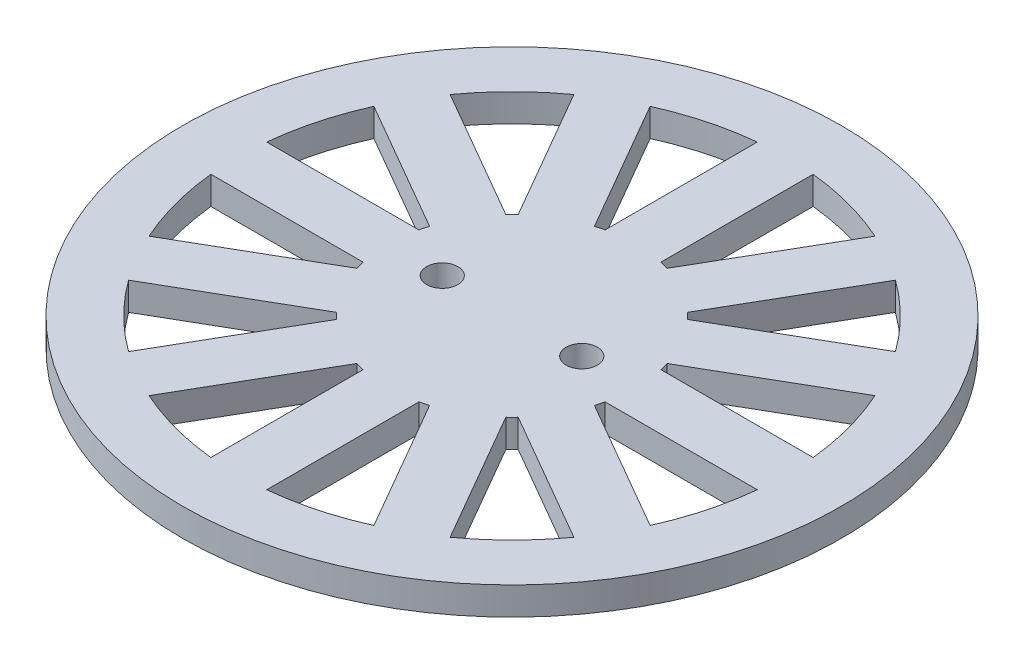
SolidWorks part; units mm, degrees
ref_plane "Front Plane" through (0, 0, 0) normal (0, 0, 1) x (1, 0, 0)
ref_plane "Top Plane" through (0, 0, 0) normal (0, 1, 0) x (1, 0, 0)
ref_plane "Right Plane" through (0, 0, 0) normal (1, 0, 0) x (0, 0, -1)
sketch "Sketch1" plane through (0, 0, 0) normal (0, 1, 0) x (1, 0, 0)
  line L0 (-2.54, 24.8706) -> (-2.54, 11.0171)
  line L1 (2.54, 24.8706) -> (2.54, 11.0171)
  line L2 (10.2356, 22.8086) -> (3.3089, 10.8111)
  line L3 (14.635, 20.2686) -> (7.7083, 8.2711)
  line L4 (20.2686, 14.635) -> (8.2711, 7.7083)
  line L5 (22.8086, 10.2356) -> (10.8111, 3.3089)
  line L6 (24.8706, 2.54) -> (11.0171, 2.54)
  line L7 (24.8706, -2.54) -> (11.0171, -2.54)
  line L8 (22.8086, -10.2356) -> (10.8111, -3.3089)
  line L9 (20.2686, -14.635) -> (8.2711, -7.7083)
  line L10 (14.635, -20.2686) -> (7.7083, -8.2711)
  line L11 (10.2356, -22.8086) -> (3.3089, -10.8111)
  line L12 (2.54, -24.8706) -> (2.54, -11.0171)
  line L13 (-2.54, -24.8706) -> (-2.54, -11.0171)
  line L14 (-10.2356, -22.8086) -> (-3.3089, -10.8111)
  line L15 (-14.635, -20.2686) -> (-7.7083, -8.2711)
  line L16 (-20.2686, -14.635) -> (-8.2711, -7.7083)
  line L17 (-22.8086, -10.2356) -> (-10.8111, -3.3089)
  line L18 (-24.8706, -2.54) -> (-11.0171, -2.54)
  line L19 (-24.8706, 2.54) -> (-11.0171, 2.54)
  line L20 (-22.8086, 10.2356) -> (-10.8111, 3.3089)
  line L21 (-20.2686, 14.635) -> (-8.2711, 7.7083)
  line L22 (-14.635, 20.2686) -> (-7.7083, 8.2711)
  line L23 (-10.2356, 22.8086) -> (-3.3089, 10.8111)
  circle A0 centre (0, 0) radius 30
  arc A1 (10.2356, 22.8086) -> (2.54, 24.8706) centre (0, 0) ccw
  circle A2 centre (0, 0) radius 11.3061
  circle A3 centre (6.35, 0) radius 1.4224
  circle A4 centre (-6.35, 0) radius 1.4224
  arc A5 (-2.54, 24.8706) -> (-10.2356, 22.8086) centre (0, 0) ccw
  arc A6 (-14.635, 20.2686) -> (-20.2686, 14.635) centre (0, 0) ccw
  arc A7 (-22.8086, 10.2356) -> (-24.8706, 2.54) centre (0, 0) ccw
  arc A8 (-24.8706, -2.54) -> (-22.8086, -10.2356) centre (0, 0) ccw
  arc A9 (-20.2686, -14.635) -> (-14.635, -20.2686) centre (0, 0) ccw
  arc A10 (-10.2356, -22.8086) -> (-2.54, -24.8706) centre (0, 0) ccw
  arc A11 (2.54, -24.8706) -> (10.2356, -22.8086) centre (0, 0) ccw
  arc A12 (14.635, -20.2686) -> (20.2686, -14.635) centre (0, 0) ccw
  arc A13 (22.8086, -10.2356) -> (24.8706, -2.54) centre (0, 0) ccw
  arc A14 (24.8706, 2.54) -> (22.8086, 10.2356) centre (0, 0) ccw
  arc A15 (20.2686, 14.635) -> (14.635, 20.2686) centre (0, 0) ccw
  point P59 (0, 0)
  dimension "D1" = 6.35
  dimension "D3" = 2.8448
  dimension "D4" = 2.8448
  dimension "D5" = 2.54
  dimension "D8" = 60
  dimension "D9" = 25
  dimension "D2" = 6.35
  dimension "D6" = 2.54
  dimension "D7" = 12
extrude "Boss-Extrude1" add sketch "Sketch1" along normal blind 2.54 contours A0 A15 L4 A2 L5 A14 L6 L7 A13 L8 L9 A12 L10 L11 A11 L12 L13 A10 L14 L15 A9 L16 L17 A8 L18 L19 A7 L20 L21 A6 L22 L23 A5 L0 L1 A1 L2 L3 | A2 A4 A3
